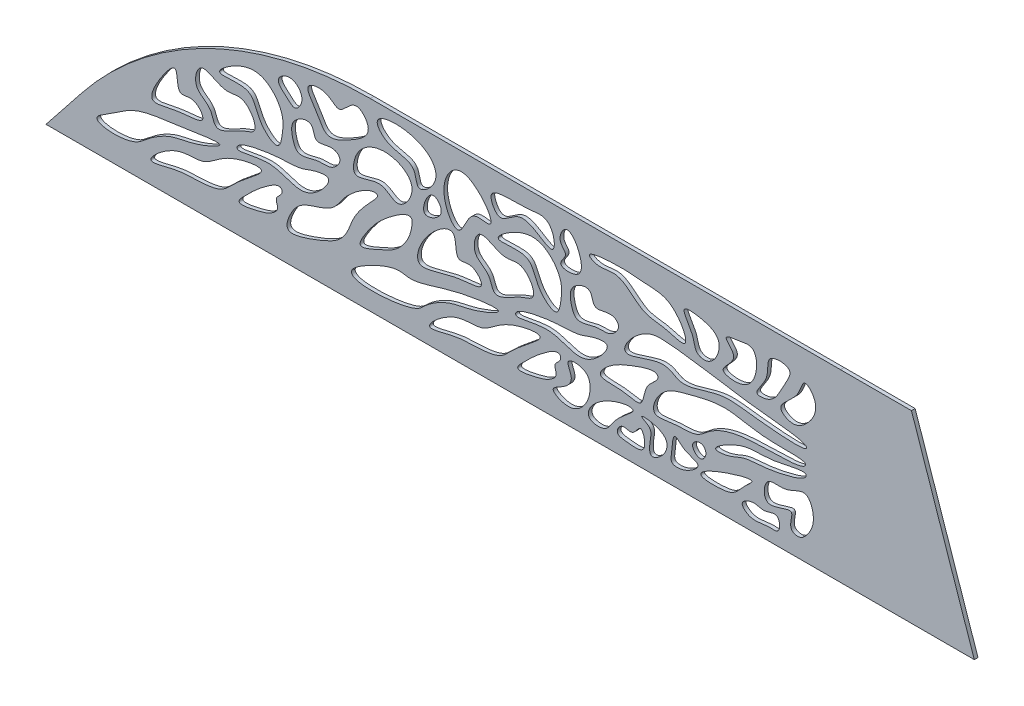
SolidWorks part; units mm, degrees
ref_plane "Alzado" through (0, 0, 0) normal (0, 0, 1) x (1, 0, 0)
ref_plane "Planta" through (0, 0, 0) normal (0, 1, 0) x (1, 0, 0)
ref_plane "Vista lateral" through (0, 0, 0) normal (1, 0, 0) x (0, 0, -1)
sketch "Croquis2" plane through (0, 0, 0) normal (0, 0, 1) x (1, 0, 0)
  line L0 (-150.6348, 4.2811) -> (81.9745, 4.4283)
  line L1 (-62.6667, 54.3368) -> (64.9165, 54.4175)
  line L3 (-150.6348, 4.2811) -> (-140.9234, 16.5138)
  line L4 (64.9165, 54.4175) -> (84.1799, 54.4175)
  line L5 (84.1799, 54.4175) -> (101.2379, 4.4283)
  line L6 (101.2379, 4.4283) -> (81.9745, 4.4283)
  arc A0 (-55.307, 34.7188) -> (-54.8769, 34.7256) centre (-55.1234, 36.7103) ccw
  arc A1 (-140.9234, 16.5138) -> (-62.6667, 54.3368) centre (-62.6034, -45.6632) cw
  spline S0 degree 3 poles (-51.0785, 33.7126) (-51.5293, 27.3426) (-54.4547, 22.5418) (-60.0394, 20.0943) (-67.0906, 17.0171) (-62.4611, 24.397) (-58.823, 28.4133) (-51.0785, 33.7126) (-51.5293, 27.3426) (-54.4547, 22.5418) knots -0.382897 -0.210386 -0.021039 0 0.224721 0.375822 0.501741 0.617103 0.789614 0.978961 1 1.224721 1.375822 1.501741 only from (-51.3297, 30.3291) to (-51.3297, 30.3291)
  spline S1 degree 3 poles (-87.1963, 22.3052) (-86.2357, 19.8148) (-89.3671, 18.1164) (-86.9166, 16.0539) (-89.8627, 13.6185) (-93.3839, 12.5346) (-100.0716, 11.1966) (-96.0609, 15.0524) (-92.7832, 18.3807) (-87.1963, 22.3052) (-86.2357, 19.8148) (-89.3671, 18.1164) knots -0.316899 -0.167029 -0.016703 0 0.100038 0.223753 0.272835 0.361932 0.526926 0.683101 0.832971 0.983297 1 1.100038 1.223753 1.272835 only from (-86.5751, 20.5973) to (-86.5751, 20.5973)
  spline S2 degree 3 poles (-62.4058, 33.5366) (-59.5689, 32.0619) (-66.0762, 27.7246) (-69.4214, 17.8258) (-73.6808, 15.1837) (-78.0102, 13.5156) (-86.6704, 10.4723) (-83.676, 18.4084) (-80.5778, 20.9146) (-72.8596, 22.7327) (-68.5743, 29.7266) (-62.4058, 33.5366) (-59.5689, 32.0619) (-66.0762, 27.7246) knots -0.211124 -0.180844 -0.020094 0 0.139538 0.165887 0.263491 0.357788 0.4888 0.56575 0.697202 0.788876 0.819156 0.979906 1 1.139538 1.165887 1.263491 only from (-60.7374, 32.5644) to (-60.7374, 32.5644)
  spline S3 degree 3 poles (-117.6072, 21.2617) (-98.8424, 24.5763) (-110.6955, 19.2918) (-116.9041, 18.9012) (-122.5962, 15.2229) (-127.7824, 10.3685) (-140.6365, 11.2695) (-132.4148, 15.8573) (-126.1527, 20.7275) (-117.6072, 21.2617) (-98.8424, 24.5763) (-110.6955, 19.2918) knots -0.414034 -0.328547 -0.140908 0 0.101307 0.208688 0.319856 0.369897 0.539759 0.585966 0.671453 0.859092 1 1.101307 1.208688 1.319856 only from (-103.4714, 23.0105) to (-103.4714, 23.0105)
  spline S4 degree 3 poles (-98.7099, 26.4715) (-98.9066, 23.3817) (-87.8117, 27.7792) (-80.6797, 19.9629) (-71.9662, 30.6208) (-77.8972, 29.9602) (-81.651, 28.0667) (-88.1155, 28.3532) (-98.7099, 26.4715) (-98.9066, 23.3817) (-87.8117, 27.7792) knots -0.352515 -0.233319 -0.023332 0 0.173914 0.388453 0.503873 0.557099 0.647485 0.766681 0.976668 1 1.173914 1.388453 1.503873 only from (-98.7582, 24.5746) to (-98.7582, 24.5746)
  spline S5 degree 3 poles (-102.3081, 21.8701) (-87.3823, 24.6206) (-98.8046, 17.2363) (-102.5767, 12.2396) (-109.4025, 11.5015) (-114.7194, 11.7445) (-125.8254, 8.0761) (-115.3699, 17.4201) (-107.4742, 15.6363) (-102.3081, 21.8701) (-87.3823, 24.6206) (-98.8046, 17.2363) knots -0.367107 -0.25575 -0.136452 0 0.137667 0.216153 0.304697 0.407967 0.504226 0.632893 0.74425 0.863548 1 1.137667 1.216153 1.304697 only from (-92.2057, 22.7148) to (-92.2057, 22.7148)
  spline S6 degree 3 poles (-110.5182, 30.9909) (-105.9809, 25.482) (-115.0114, 25.866) (-123.8562, 22.4661) (-120.1959, 30.3136) (-114.4533, 37.5901) (-115.4943, 28.5172) (-110.5182, 30.9909) (-105.9809, 25.482) (-115.0114, 25.866) knots -0.318196 -0.189853 -0.107336 0 0.165541 0.363113 0.543334 0.681804 0.810147 0.892664 1 1.165541 1.363113 1.543334 only from (-108.0735, 27.0731) to (-108.0735, 27.0731)
  spline S7 degree 3 poles (-109.0562, 41.3372) (-110.9909, 32.558) (-105.8321, 31.2033) (-104.7454, 24.4571) (-98.8313, 29.3984) (-92.206, 30.7102) (-96.6202, 38.3282) (-102.5986, 35.3502) (-109.0562, 41.3372) (-110.9909, 32.558) (-105.8321, 31.2033) knots -0.386578 -0.279046 -0.113752 0 0.122948 0.197231 0.379613 0.462451 0.613422 0.720954 0.886248 1 1.122948 1.197231 1.379613 only from (-109.7767, 33.7145) to (-109.7767, 33.7145)
  spline S8 degree 3 poles (-97.18, 45.7132) (-107.6346, 38.238) (-94.0445, 41.4335) (-93.8154, 34.148) (-87.3693, 28.9867) (-86.3926, 34.5613) (-86.007, 39.1981) (-90.399, 45.0113) (-97.18, 45.7132) (-107.6346, 38.238) (-94.0445, 41.4335) knots -0.433573 -0.287889 -0.156313 0 0.150869 0.294545 0.406379 0.468937 0.566427 0.712111 0.843687 1 1.150869 1.294545 1.406379 only from (-103.4714, 40.0641) to (-103.4714, 40.0641)
  spline S9 degree 3 poles (-85.1871, 48.8539) (-88.9085, 46.0887) (-85.5557, 43.5954) (-83.0216, 41.0603) (-80.5301, 44.4214) (-81.97, 47.6701) (-85.1871, 48.8539) (-88.9085, 46.0887) (-85.5557, 43.5954) knots -0.501621 -0.314025 -0.1649 0 0.21872 0.339791 0.498379 0.685975 0.8351 1 1.21872 1.339791 1.498379 only from (-87.5665, 46.3858) to (-87.5665, 46.3858)
  spline S10 degree 3 poles (-78.0791, 41.7224) (-84.2636, 39.3305) (-84.0304, 35.181) (-82.377, 30.4094) (-77.2299, 33.1496) (-73.0215, 32.1164) (-69.9821, 35.7427) (-73.2167, 38.4626) (-77.8702, 35.4822) (-78.0791, 41.7224) (-84.2636, 39.3305) (-84.0304, 35.181) knots -0.366782 -0.218958 -0.135905 0 0.118786 0.203725 0.369298 0.472855 0.583849 0.633218 0.781042 0.864095 1 1.118786 1.203725 1.369298 only from (-83.1994, 38.8368) to (-83.1994, 38.8368)
  spline S11 degree 3 poles (-74.3598, 50.5295) (-81.5351, 49.4189) (-77.0011, 44.123) (-74.7036, 38.3711) (-67.8097, 41.9327) (-61.0654, 46.1064) (-67.0584, 52.9278) (-70.7617, 45.7546) (-74.3598, 50.5295) (-81.5351, 49.4189) (-77.0011, 44.123) knots -0.333304 -0.204561 -0.119166 0 0.116134 0.234719 0.387508 0.559608 0.666696 0.795439 0.880834 1 1.116134 1.234719 1.387508 only from (-79.4795, 48.7142) to (-79.4795, 48.7142)
  spline S12 degree 3 poles (15.1674, 29.5803) (15.5447, 26.8647) (11.3584, 24.6832) (11.697, 19.0605) (8.464, 19.2485) (4.8561, 20.2047) (-2.2577, 19.4899) (2.2568, 24.3884) (7.0492, 26.68) (15.1674, 29.5803) (15.5447, 26.8647) (11.3584, 24.6832) knots -0.316899 -0.167029 -0.016703 0 0.100038 0.223753 0.272835 0.361932 0.526926 0.683101 0.832971 0.983297 1 1.100038 1.223753 1.272835 only from (15.382, 27.7147) to (15.382, 27.7147)
  spline S13 degree 3 poles (55.5501, 23.2619) (55.7078, 26.189) (44.178, 22.6293) (39.3548, 24.7874) (28.8738, 18.3098) (34.9887, 18.7598) (38.5886, 20.9573) (45.108, 20.8226) (55.5501, 23.2619) (55.7078, 26.189) (44.178, 22.6293) knots -0.352515 -0.233319 -0.023332 0 0.173914 0.388453 0.503873 0.557099 0.647485 0.766681 0.976668 1 1.173914 1.388453 1.503873 only from (55.5712, 25.0629) to (55.5712, 25.0629)
  spline S14 degree 3 poles (54.2419, 25.1994) (56.2819, 28.5049) (42.7606, 27.5235) (34.2775, 30.7586) (24.1149, 28.1128) (15.8619, 26.0028) (12.7353, 17.6843) (20.543, 19.5229) (25.7548, 18.7984) (30.0665, 23.1256) (39.1287, 26.6195) (54.2419, 25.1994) (56.2819, 28.5049) (42.7606, 27.5235) knots -0.295039 -0.191816 -0.019182 0 0.11455 0.24602 0.351314 0.440261 0.51992 0.570513 0.65581 0.704961 0.808184 0.980818 1 1.11455 1.24602 1.351314 only from (55.4883, 27.4361) to (55.4883, 27.4361)
  spline S15 degree 3 poles (57.012, 30.2014) (54.6555, 32.8339) (38.2593, 33.8974) (23.6196, 37.1267) (10.4754, 37.6289) (1.9199, 25.9954) (17.7457, 33.2536) (21.1866, 27.865) (32.1648, 33.2277) (40.3095, 31.5112) (57.012, 30.2014) (54.6555, 32.8339) (38.2593, 33.8974) knots -0.2879 -0.155387 -0.015539 0 0.099677 0.267068 0.297768 0.406678 0.472741 0.561818 0.7121 0.844613 0.984461 1 1.099677 1.267068 1.297768 only from (55.3306, 31.9518) to (55.3306, 31.9518)
  spline S16 degree 3 poles (43.6493, 10.2591) (44.2303, 19.8155) (50.3447, 17.7374) (55.8529, 22.5361) (58.2511, 15.5439) (56.6052, 11.7655) (54.0863, 8.9997) (50.4494, 10.1957) (53.6882, 17.0375) (43.6493, 10.2591) (44.2303, 19.8155) (50.3447, 17.7374) knots -0.371419 -0.276319 -0.113656 0 0.115773 0.264232 0.386481 0.50234 0.57949 0.628581 0.723681 0.886344 1 1.115773 1.264232 1.386481 only from (45.0547, 18.082) to (45.0547, 18.082)
  spline S17 degree 3 poles (6.5797, 49.0715) (-5.1998, 47.9969) (-0.3427, 45.3757) (5.3186, 47.9432) (10.5937, 40.4782) (16.8374, 40.8325) (25.2525, 37.4599) (19.7387, 48.1682) (11.6721, 47.98) (6.5797, 49.0715) (-5.1998, 47.9969) (-0.3427, 45.3757) knots -0.391213 -0.273847 -0.12925 0 0.018174 0.122894 0.279654 0.384629 0.472626 0.608787 0.726153 0.87075 1 1.018174 1.122894 1.279654 only from (-2.9266, 46.8272) to (-2.9266, 46.8272)
  spline S18 degree 3 poles (28.0106, 47.6298) (20.3036, 48.4786) (25.3708, 42.896) (25.3219, 38.6925) (30.3662, 37.5023) (33.7492, 45.0865) (28.0106, 47.6298) (20.3036, 48.4786) (25.3708, 42.896) knots -0.597987 -0.351672 -0.165698 0 0.195722 0.325152 0.402013 0.648328 0.834302 1 1.195722 1.325152 1.402013 only from (22.5801, 47.4503) to (22.5801, 47.4503)
  spline S19 degree 3 poles (37.5341, 47.4197) (32.1879, 46.7772) (38.6348, 42.6518) (30.7702, 38.3189) (37.488, 36.7678) (42.4289, 39.384) (42.5859, 48.6024) (37.5341, 47.4197) (32.1879, 46.7772) (38.6348, 42.6518) knots -0.438785 -0.218352 -0.095301 0 0.113934 0.288077 0.377524 0.561215 0.781648 0.904699 1 1.113934 1.288077 1.377524 only from (33.916, 46.4301) to (33.916, 46.4301)
  spline S20 degree 3 poles (52.8853, 48.398) (43.9225, 48.5488) (46.4239, 42.3923) (40.5934, 37.0889) (47.0664, 37.3745) (48.5877, 41.7261) (52.8853, 48.398) (43.9225, 48.5488) (46.4239, 42.3923) knots -0.577089 -0.309658 -0.16535 0 0.184162 0.363281 0.422911 0.690342 0.83465 1 1.184162 1.363281 1.422911 only from (46.0538, 47.6081) to (46.0538, 47.6081)
  spline S21 degree 3 poles (52.1024, 34.5883) (46.2239, 37.8354) (53.711, 41.0077) (54.7358, 47.7119) (59.7374, 42.8441) (56.6937, 37.249) (52.1024, 34.5883) (46.2239, 37.8354) (53.711, 41.0077) knots -0.509276 -0.239068 -0.105487 0 0.2678 0.390798 0.490724 0.760932 0.894513 1 1.2678 1.390798 1.490724 only from (48.9018, 36.7952) to (48.9018, 36.7952)
  spline S22 degree 3 poles (44.1907, 10.304) (48.5607, 12.885) (48.7131, 7.4727) (44.2276, 8.0897) (40.9938, 6.3748) (37.2572, 10.0153) (41.4569, 11.995) (44.1907, 10.304) (48.5607, 12.885) (48.7131, 7.4727) knots -0.419869 -0.272796 -0.144259 0 0.160267 0.210766 0.504987 0.580131 0.727204 0.855741 1 1.160267 1.210766 1.504987 only from (47.7389, 11.3406) to (47.7389, 11.3406)
  spline S23 degree 3 poles (33.4428, 14.6378) (25.95, 11.3591) (26.0955, 9.834) (33.7564, 10.225) (36.6735, 11.0547) (38.3373, 13.6855) (43.1592, 17.6899) (33.4428, 14.6378) (25.95, 11.3591) (26.0955, 9.834) knots -0.368151 -0.318593 -0.092466 0 0.381238 0.430835 0.495972 0.631849 0.681407 0.907534 1 1.381238 1.430835 1.495972 only from (29.24, 12.744) to (29.24, 12.744)
  spline S24 degree 3 poles (-0.5094, 16.2335) (-5.3476, 8.511) (1.47, 7.8354) (3.5308, 12.1023) (6.1278, 14.1148) (10.8145, 18.1553) (-0.5094, 16.2335) (-5.3476, 8.511) (1.47, 7.8354) knots -0.566614 -0.504093 -0.218818 0 0.131217 0.261968 0.433386 0.495907 0.781182 1 1.131217 1.261968 1.433386 only from (-3.0333, 8.9167) to (-3.0333, 8.9167)
  spline S25 degree 3 poles (8.7137, 10.3177) (5.604, 12.4546) (3.5186, 8.7676) (7.9192, 8.3885) (12.9091, 7.7165) (10.9201, 15.5155) (8.7137, 10.3177) (5.604, 12.4546) (3.5186, 8.7676) knots -0.50021 -0.292274 -0.145876 0 0.117021 0.265473 0.49979 0.707726 0.854124 1 1.117021 1.265473 1.49979 only from (5.5894, 11.4571) to (5.5894, 11.4571)
  spline S26 degree 3 poles (19.2587, 16.2067) (8.5062, 17.1744) (14.1085, 14.9015) (13.1085, 11.9197) (12.9944, 7.5208) (17.5285, 10.1658) (19.2587, 16.2067) (8.5062, 17.1744) (14.1085, 14.9015) knots -0.618588 -0.487424 -0.262237 0 0.100832 0.255151 0.381412 0.512576 0.737763 1 1.100832 1.255151 1.381412 only from (11.069, 16.2963) to (11.069, 16.2963)
  spline S27 degree 3 poles (22.5995, 13.7051) (19.4416, 17.8074) (19.3001, 12.8088) (18.4493, 8.9609) (23.368, 9.3021) (28.0126, 13.3168) (22.5995, 13.7051) (19.4416, 17.8074) (19.3001, 12.8088) knots -0.521013 -0.326779 -0.141819 0 0.174988 0.298356 0.478987 0.673221 0.858181 1 1.174988 1.298356 1.478987 only from (20.0295, 16.2963) to (20.0295, 16.2963)
  spline S28 degree 3 poles (27.4869, 18.8981) (23.4379, 17.0437) (26.8483, 13.4144) (28.8991, 16.2041) (27.4869, 18.8981) (23.4379, 17.0437) (26.8483, 13.4144) knots -0.695992 -0.473766 -0.274772 0 0.304008 0.526234 0.725228 1 1.304008 1.526234 1.725228 only from (24.8246, 16.8334) to (24.8246, 16.8334)
  spline S29 degree 3 poles (-9.6929, 12.7725) (-14.6607, 10.8611) (-8.9253, 7.9804) (-4.6152, 10.3619) (-2.6409, 14.9324) (-3.3536, 20.209) (-10.4961, 20.4048) (-7.1657, 15.7456) (-9.6929, 12.7725) (-14.6607, 10.8611) (-8.9253, 7.9804) knots -0.317976 -0.224175 -0.099552 0 0.115791 0.261606 0.42371 0.543191 0.682024 0.775825 0.900448 1 1.115791 1.261606 1.42371 only from (-13.02, 10.844) to (-13.02, 10.844)
  spline S30 degree 3 poles (-11.6004, 21.0112) (-10.6397, 18.5207) (-13.7711, 16.8223) (-11.3207, 14.7599) (-14.2667, 12.3244) (-17.788, 11.2406) (-24.4756, 9.9025) (-20.465, 13.7584) (-17.1872, 17.0867) (-11.6004, 21.0112) (-10.6397, 18.5207) (-13.7711, 16.8223) knots -0.316899 -0.167029 -0.016703 0 0.100038 0.223753 0.272835 0.361932 0.526926 0.683101 0.832971 0.983297 1 1.100038 1.223753 1.272835 only from (-10.9792, 19.3032) to (-10.9792, 19.3032)
  spline S31 degree 3 poles (-56.8579, 45.4432) (-66.5087, 42.8926) (-67.8908, 32.0763) (-59.8416, 37.5552) (-54.8934, 31.1826) (-49.3878, 39.1154) (-56.8579, 45.4432) (-66.5087, 42.8926) (-67.8908, 32.0763) knots -0.603799 -0.439248 -0.299571 0 0.101141 0.280469 0.396201 0.560752 0.700429 1 1.101141 1.280469 1.396201 only from (-66.5865, 38.8368) to (-66.5865, 38.8368)
  spline S32 degree 3 poles (-41.8585, 20.8028) (-23.26, 23.1492) (-35.1253, 18.0251) (-41.1789, 17.6217) (-47.3898, 13.8578) (-51.0233, 9.2888) (-76.6784, 7.8234) (-56.0398, 18.6876) (-51.1668, 16.2006) (-41.8585, 20.8028) (-23.26, 23.1492) (-35.1253, 18.0251) knots -0.414034 -0.328547 -0.140908 0 0.101307 0.208688 0.319856 0.369897 0.539759 0.585966 0.671453 0.859092 1 1.101307 1.208688 1.319856 only from (-27.8755, 21.7164) to (-27.8755, 21.7164)
  spline S33 degree 3 poles (-23.1139, 25.1774) (-23.3107, 22.0876) (-12.2158, 26.4851) (-5.0837, 18.6688) (3.6298, 29.3267) (-2.3013, 28.6661) (-6.0551, 26.7727) (-12.5195, 27.0591) (-23.1139, 25.1774) (-23.3107, 22.0876) (-12.2158, 26.4851) knots -0.352515 -0.233319 -0.023332 0 0.173914 0.388453 0.503873 0.557099 0.647485 0.766681 0.976668 1 1.173914 1.388453 1.503873 only from (-23.1622, 23.2805) to (-23.1622, 23.2805)
  spline S34 degree 3 poles (-26.7121, 20.576) (-11.7864, 23.3266) (-23.2087, 15.9423) (-26.9808, 10.9455) (-33.8065, 10.2074) (-39.1234, 10.4505) (-50.2295, 6.7821) (-39.7739, 16.126) (-31.8783, 14.3423) (-26.7121, 20.576) (-11.7864, 23.3266) (-23.2087, 15.9423) knots -0.367107 -0.25575 -0.136452 0 0.137667 0.216153 0.304697 0.407967 0.504226 0.632893 0.74425 0.863548 1 1.137667 1.216153 1.304697 only from (-16.6097, 21.4207) to (-16.6097, 21.4207)
  spline S35 degree 3 poles (-34.9213, 29.6533) (-30.3962, 24.2002) (-41.0892, 24.7061) (-51.3391, 19.2578) (-48.5545, 29.9832) (-38.5742, 37.6412) (-39.8962, 27.3783) (-34.9213, 29.6533) (-30.3962, 24.2002) (-41.0892, 24.7061) knots -0.26949 -0.160792 -0.090906 0 0.140202 0.385455 0.525796 0.73051 0.839208 0.909094 1 1.140202 1.385455 1.525796 only from (-32.4775, 25.779) to (-32.4775, 25.779)
  spline S36 degree 3 poles (-33.4603, 40.0431) (-35.395, 31.2639) (-30.2361, 29.9092) (-29.1494, 23.163) (-23.2353, 28.1044) (-16.6101, 29.4161) (-21.0242, 37.0341) (-27.0027, 34.0562) (-33.4603, 40.0431) (-35.395, 31.2639) (-30.2361, 29.9092) knots -0.386578 -0.279046 -0.113752 0 0.122948 0.197231 0.379613 0.462451 0.613422 0.720954 0.886248 1 1.122948 1.197231 1.379613 only from (-34.1808, 32.4205) to (-34.1808, 32.4205)
  spline S37 degree 3 poles (-21.5841, 44.4191) (-32.0386, 36.9439) (-18.4485, 40.1394) (-18.2195, 32.8539) (-11.7734, 27.6926) (-10.7967, 33.2672) (-10.411, 37.9041) (-14.803, 43.7172) (-21.5841, 44.4191) (-32.0386, 36.9439) (-18.4485, 40.1394) knots -0.433573 -0.287889 -0.156313 0 0.150869 0.294545 0.406379 0.468937 0.566427 0.712111 0.843687 1 1.150869 1.294545 1.406379 only from (-27.8755, 38.7701) to (-27.8755, 38.7701)
  spline S38 degree 3 poles (-2.4832, 40.4283) (-8.6677, 38.0364) (-8.4344, 33.8869) (-6.7811, 29.1153) (-1.6339, 31.8556) (2.5745, 30.8223) (5.6138, 34.4487) (2.3792, 37.1685) (-2.2743, 34.1881) (-2.4832, 40.4283) (-8.6677, 38.0364) (-8.4344, 33.8869) knots -0.366782 -0.218958 -0.135905 0 0.118786 0.203725 0.369298 0.472855 0.583849 0.633218 0.781042 0.864095 1 1.118786 1.203725 1.369298 only from (-7.6034, 37.5427) to (-7.6034, 37.5427)
  spline S39 degree 3 poles (-48.8622, 52.9771) (-63.8386, 51.9195) (-56.9902, 44.6391) (-50.3749, 45.8541) (-50.1038, 38.0736) (-42.4148, 44.446) (-48.8622, 52.9771) (-63.8386, 51.9195) (-56.9902, 44.6391) knots -0.621375 -0.49217 -0.277193 0 0.102406 0.29911 0.378625 0.50783 0.722807 1 1.102406 1.29911 1.378625 only from (-60.7374, 49.4115) to (-60.7374, 49.4115)
  spline S40 degree 3 poles (-48.6, 33.0509) (-48.0442, 37.86) (-45.5527, 41.4921) (-41.5474, 36.3215) (-48.6, 33.0509) (-48.0442, 37.86) (-45.5527, 41.4921) knots -0.751349 -0.518378 -0.176608 0 0.248651 0.481622 0.823392 1 1.248651 1.481622 1.823392 only from (-47.872, 37.3532) to (-47.872, 37.3532)
  spline S41 degree 3 poles (-37.6083, 54.7384) (-45.0768, 42.8512) (-37.9806, 31.4422) (-36.1406, 42.3894) (-26.3996, 39.0387) (-37.6083, 54.7384) (-45.0768, 42.8512) (-37.9806, 31.4422) knots -0.618533 -0.522414 -0.241963 0 0.198572 0.381467 0.477586 0.758037 1 1.198572 1.381467 1.477586 only from (-42.6369, 41.8948) to (-42.6369, 41.8948)
  spline S42 degree 3 poles (-23.5532, 49.0905) (-32.3968, 50.8969) (-27.1564, 41.7908) (-21.4172, 50.8608) (-11.1546, 38.6809) (-13.2271, 50.7054) (-23.5532, 49.0905) (-32.3968, 50.8969) (-27.1564, 41.7908) knots -0.515833 -0.352351 -0.300768 0 0.085287 0.253991 0.484167 0.647649 0.699232 1 1.085287 1.253991 1.484167 only from (-29.8026, 46.9728) to (-29.8026, 46.9728)
  spline S43 degree 3 poles (-8.5862, 44.2119) (-12.0858, 46.4085) (-9.3621, 52.6016) (-5.0102, 45.9245) (-5.2707, 40.0318) (-12.8421, 40.5908) (-8.5862, 44.2119) (-12.0858, 46.4085) (-9.3621, 52.6016) knots -0.39577 -0.225994 -0.10263 0 0.162088 0.409403 0.60423 0.774006 0.89737 1 1.162088 1.409403 1.60423 only from (-10.9792, 46.328) to (-10.9792, 46.328)
  point P219 (51.5758, 11.3406)
  dimension "D1" = 2
  dimension "D2" = 232.6092
extrude "Saliente-Extruir1" add sketch "Croquis2" along normal blind 1
